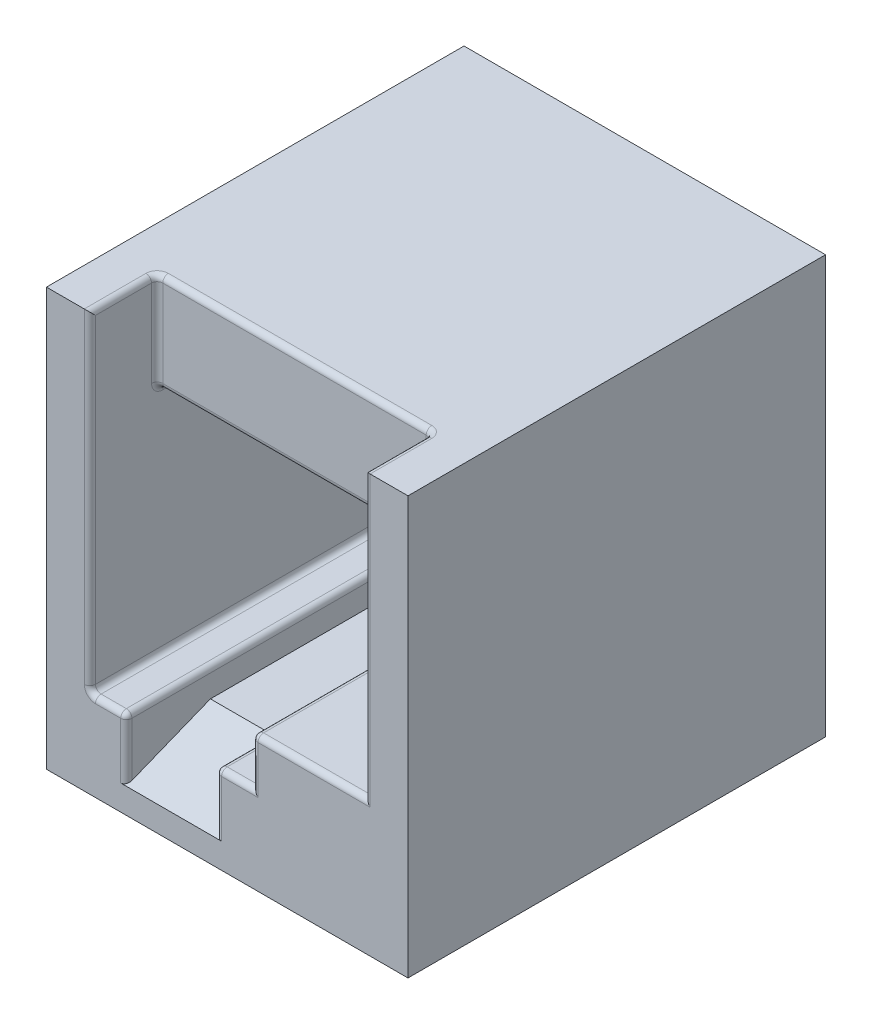
SolidWorks part; units mm, degrees
material "PVC Rigid"
ref_plane "Front Plane" through (0, 0, 0) normal (0, 0, 1) x (1, 0, 0)
ref_plane "Top Plane" through (0, 0, 0) normal (0, 1, 0) x (1, 0, 0)
ref_plane "Right Plane" through (0, 0, 0) normal (1, 0, 0) x (0, 0, -1)
sketch "Sketch1" plane through (0, 0, 0) normal (0, 0, 1) x (1, 0, 0)
  line L1 (0, 0) -> (12.9, 0)
  line L2 (0, 0) -> (0, 14.9)
  line L3 (0, 14.9) -> (12.9, 14.9)
  line L4 (12.9, 0) -> (12.9, 14.9)
  dimension "D1" = 12.9
  dimension "D2" = 14.9
extrude "Extrude1" add sketch "Sketch1" against normal blind 14.9
sketch "Sketch2" plane through (0, 0, 0) normal (0, 0, 1) x (1, 0, 0)
  line L0 (12.9, 14.9) -> (0, 14.9) construction
  line L1 (1.55, 14.9) -> (11.35, 14.9)
  line L2 (1.55, 14.9) -> (1.55, 11.4)
  line L3 (1.55, 11.4) -> (11.35, 11.4)
  line L4 (11.35, 14.9) -> (11.35, 11.4)
  line L6 (0, 14.9) -> (0, 0) construction
  dimension "D1" = 9.8
  dimension "D2" = 3.5
  dimension "D3" = 1.55
extrude "Extrude2" cut sketch "Sketch2" against normal blind 2.4
sketch "Sketch3" plane through (0, 0, 0) normal (0, 0, 1) x (1, 0, 0)
  line L0 (1.55, 11.4) -> (1.55, 3.1)
  line L1 (1.55, 3.1) -> (2.85, 3.1)
  line L2 (2.85, 3.1) -> (2.85, 2.1)
  line L3 (2.85, 2.1) -> (6.05, 2.1)
  line L4 (6.05, 2.1) -> (6.05, 3.1)
  line L5 (6.05, 3.1) -> (7.35, 3.1)
  line L6 (7.35, 3.1) -> (7.35, 4.8)
  line L7 (7.35, 4.8) -> (11.35, 4.8)
  line L8 (11.35, 4.8) -> (11.35, 11.4)
  line L9 (11.35, 11.4) -> (1.55, 11.4)
  line L10 (11.35, 14.9) -> (1.55, 14.9) construction
  dimension "D1" = 4
  dimension "D2" = 1.3
  dimension "D3" = 3.2
  dimension "D4" = 6.6
  dimension "D5" = 11.8
  dimension "D6" = 12.8
extrude "Extrude3" cut sketch "Sketch3" against normal blind 12.5
chamfer "Chamfer1" distance 1.2 distance2 3 1 edges at (4.45, 2.1, 0)
fillet "Fillet1" radius 0.2 29 edges at (11.35, 14.9, -1.2) (11.35, 11.4, -7.45) (6.45, 14.9, -2.4) (1.55, 11.4, -7.45) (2.85, 2, 0) (6.05, 2, 0) (6.7, 3.1, 0) (7.35, 3.95, 0) (9.35, 4.8, 0) (11.35, 9.85, 0) (11.35, 13.15, -2.4) (1.55, 13.15, -2.4) (6.45, 11.4, -2.4) (1.55, 14.9, -1.2) (1.55, 9, 0) (2.2, 3.1, 0) (9.35, 4.8, -12.5) (6.05, 2.6, -12.5) (2.85, 2.6, -12.5) (1.55, 7.25, -12.5) (6.45, 11.4, -12.5) (11.35, 8.1, -12.5) (7.35, 3.95, -12.5) (6.7, 3.1, -12.5) (2.2, 3.1, -12.5) (1.55, 3.1, -6.25) (7.35, 4.8, -6.25) (6.05, 3.1, -6.25) (2.85, 3.1, -6.25)
